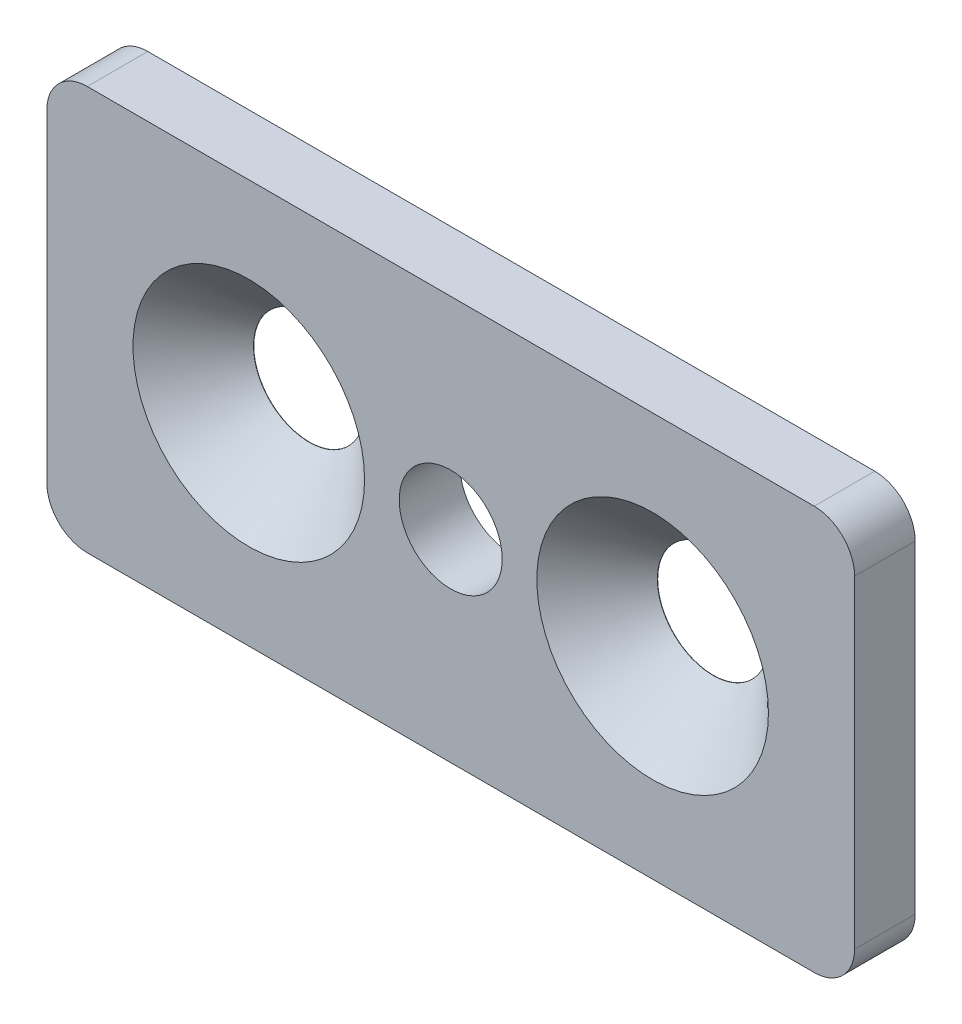
SolidWorks part; units mm, degrees
ref_plane "Alzado" through (0, 0, 0) normal (0, 0, 1) x (1, 0, 0)
ref_plane "Planta" through (0, 0, 0) normal (0, 1, 0) x (1, 0, 0)
ref_plane "Vista lateral" through (0, 0, 0) normal (1, 0, 0) x (0, 0, -1)
sketch "Croquis1" plane through (0, 0, 0) normal (0, 0, 1) x (1, 0, 0)
  line L0 (0, 10) -> (40, 10) construction
  line L1 (2, 0) -> (38, 0)
  line L2 (0, 2) -> (0, 18)
  line L3 (2, 20) -> (38, 20)
  line L4 (40, 2) -> (40, 18)
  arc A0 (2, 0) -> (0, 2) centre (2, 2) cw
  arc A1 (38, 0) -> (40, 2) centre (38, 2) ccw
  arc A2 (38, 20) -> (40, 18) centre (38, 18) cw
  arc A3 (0, 18) -> (2, 20) centre (2, 18) cw
  circle A4 centre (10, 10) radius 2.55
  circle A5 centre (20, 10) radius 2.55
  circle A6 centre (30, 10) radius 2.55
  point P7 (0, 0)
  point P12 (40, 20)
  point P15 (0, 20)
  dimension "D3" = 2
  dimension "D4" = 5.1
  dimension "D1" = 40
  dimension "D2" = 20
  dimension "D5" = 10
  dimension "D6" = 10
extrude "Saliente-Extruir1" add sketch "Croquis1" along normal blind 3
hole_wizard "Avellanado para tornillo con cabeza avellanada de clavija hexagonal de M51" positions "Croquis3" profile "Croquis2" countersink size "M5" standard "DIN"
sketch "Croquis3" plane through (0, 0, 3) normal (0, 0, 1) x (1, 0, 0)
  point P0 (10, 10)
  point P3 (30, 10)
sketch "Croquis2" plane through (10, 10, 3) normal (1, 0, 0) x (0, -1, 0)
  line L0 (0, 0) -> (0, 6.6524)
  line L1 (0, 6.6524) -> (2.75, 5)
  line L2 (2.75, 5) -> (2.75, 2.985)
  line L3 (2.75, 2.985) -> (5.735, 0)
  line L5 (5.735, 0) -> (0, 0)
  line L6 (-2.75, 2.985) -> (-5.735, 0) construction
  line L10 (0, 6.6524) -> (-2.75, 5) construction
  line L11 (0, -6.35) -> (0, 107.95) construction
  dimension "Diámetro de taladro" = 5.5
  dimension "Profundidad de taladro" = 5
  dimension "Ángulo de avellanado cercano" = 11.47
  dimension "Ángulo de avellanado lejano" = 90
  dimension "Ángulo de perforador" = 118
